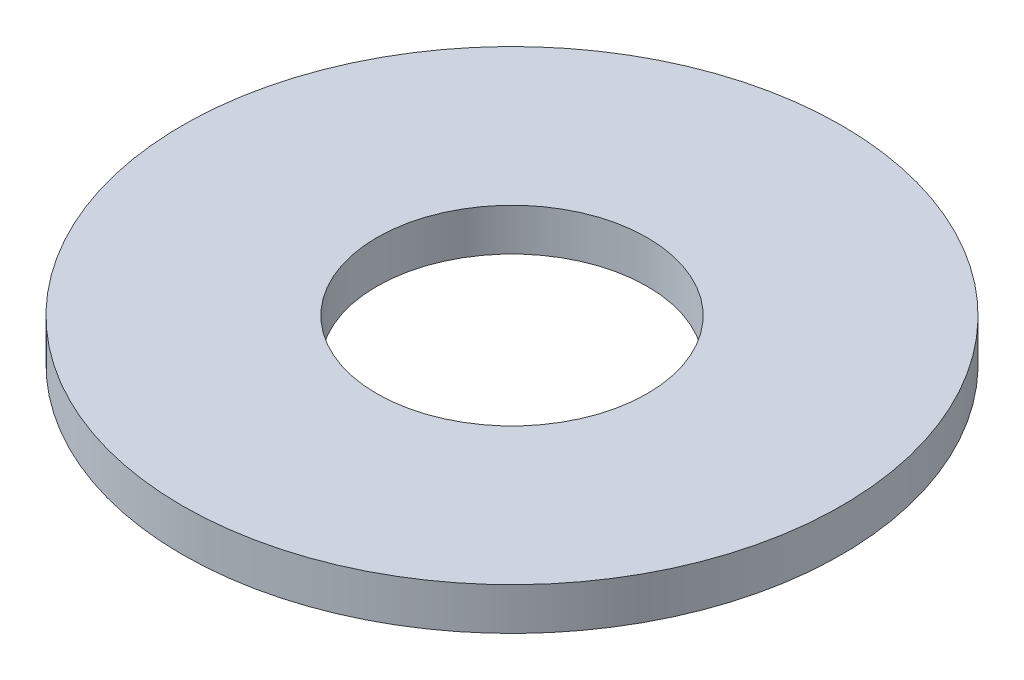
SolidWorks part; units mm, degrees
material "Cast Alloy Steel"
ref_plane "Front" through (0, 0, 0) normal (0, 0, 1) x (1, 0, 0)
ref_plane "Top" through (0, 0, 0) normal (0, 1, 0) x (1, 0, 0)
ref_plane "Right" through (0, 0, 0) normal (1, 0, 0) x (0, 0, -1)
sketch "Sketch1" plane through (0, 0, 0) normal (0, 1, 0) x (1, 0, 0)
  circle A0 centre (0, 0) radius 1.6
  circle A1 centre (0, 0) radius 3.9
  dimension "D1" = 3.2
  dimension "D2" = 7.8
extrude "Extrude1" add sketch "Sketch1" along normal blind 0.5
